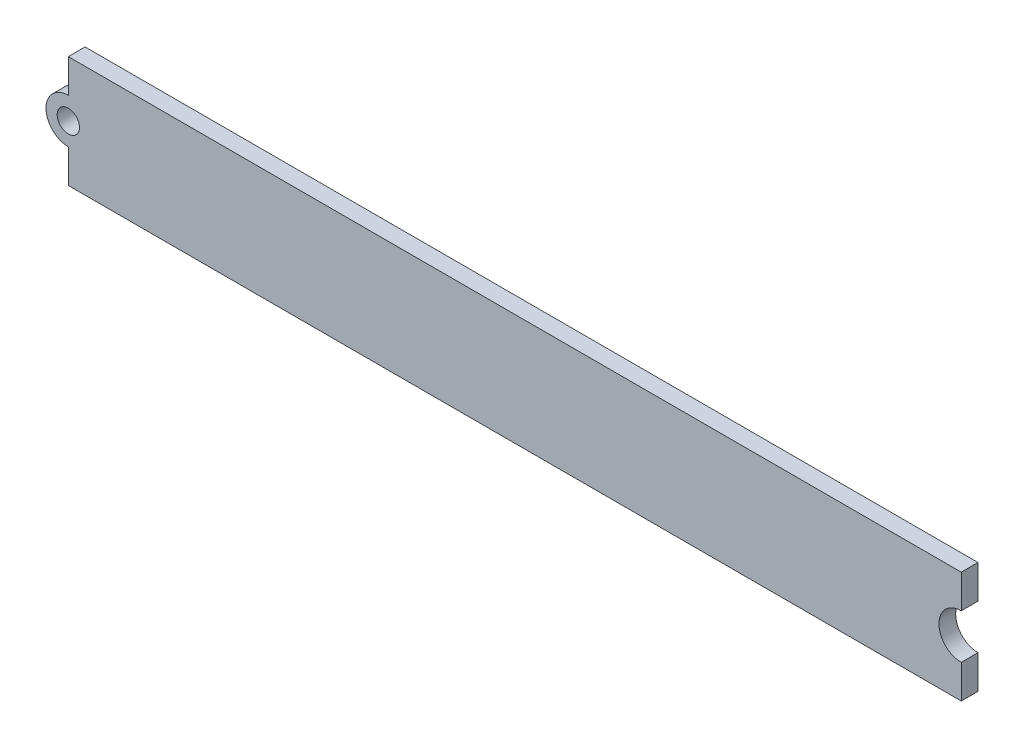
SolidWorks part; units mm, degrees
ref_plane "Plan de face" through (0, 0, 0) normal (0, 0, 1) x (1, 0, 0)
ref_plane "Plan de dessus" through (0, 0, 0) normal (0, 1, 0) x (1, 0, 0)
ref_plane "Plan de droite" through (0, 0, 0) normal (1, 0, 0) x (0, 0, -1)
sketch "Esquisse1" plane through (0, 0, 0) normal (0, 0, 1) x (1, 0, 0)
  line L0 (-50.5098, 0) -> (56.3137, 0) construction
  line L1 (0, 17.8039) -> (0, -14.1961) construction
  line L2 (-40, -2) -> (-40, -5)
  line L3 (-40, 5) -> (40, 5)
  line L4 (-40, 5) -> (-40, 2)
  line L5 (-40, -5) -> (40, -5)
  line L6 (40, 5) -> (40, 2)
  line L7 (40, -2) -> (40, -5)
  arc A0 (-40, 2) -> (-40, -2) centre (-40, 0) ccw
  circle A1 centre (-40, 0) radius 1
  arc A2 (40, 2) -> (40, -2) centre (40, 0) ccw
  dimension "D3" = 4
  dimension "D4" = 2
  dimension "D5" = 4
  dimension "D1" = 80
  dimension "D2" = 10
extrude "Boss.-Extru.1" add sketch "Esquisse1" along normal blind 1.5
